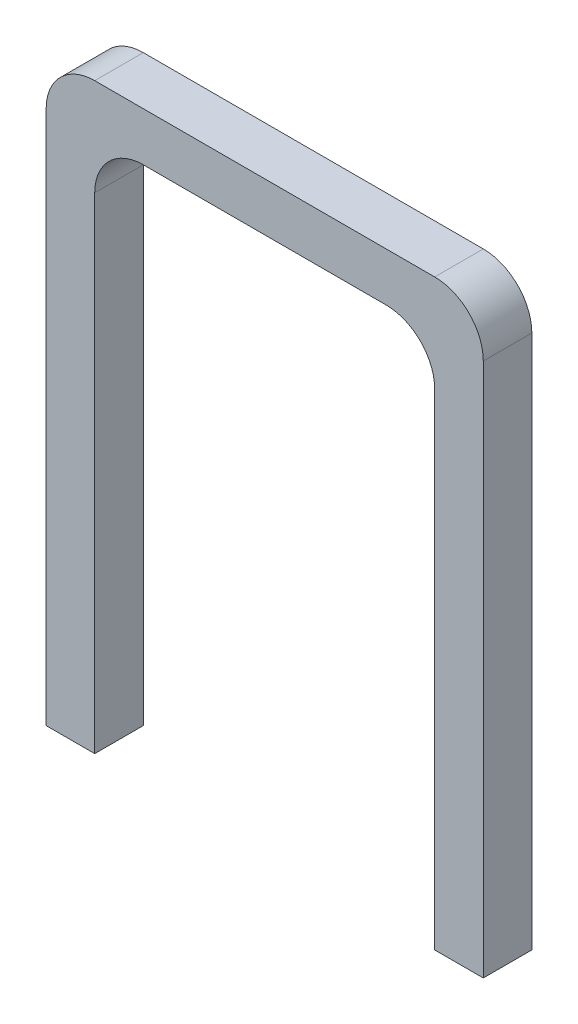
SolidWorks part; units mm, degrees
ref_plane "Front Plane" through (0, 0, 0) normal (0, 0, 1) x (1, 0, 0)
ref_plane "Top Plane" through (0, 0, 0) normal (0, 1, 0) x (1, 0, 0)
ref_plane "Right Plane" through (0, 0, 0) normal (1, 0, 0) x (0, 0, -1)
sketch "Sketch1" plane through (0, 0, 0) normal (0, 1, 0) x (1, 0, 0)
  line L1 (0, 0) -> (2, 0)
  line L2 (0, 0) -> (0, 2)
  line L3 (0, 2) -> (2, 2)
  line L4 (2, 0) -> (2, 2)
extrude "Boss-Extrude1" add sketch "Sketch1" along normal blind 24
sketch "Sketch2" plane through (2, 0, 0) normal (1, 0, 0) x (0, 0, -1)
  line L0 (2, 24) -> (2, 0) construction
  line L1 (0, 24) -> (2, 24)
  line L2 (0, 24) -> (0, 22)
  line L3 (0, 22) -> (2, 22)
  line L4 (2, 24) -> (2, 22)
  dimension "D1" = 2
extrude "Boss-Extrude2" add sketch "Sketch2" along normal blind 16
sketch "Sketch3" plane through (0, 22, 0) normal (0, -1, 0) x (-1, 0, 0)
  line L0 (-18, 2) -> (-2, 2) construction
  line L1 (-18, 0) -> (-16, 0)
  line L2 (-18, 0) -> (-18, 2)
  line L3 (-18, 2) -> (-16, 2)
  line L4 (-16, 0) -> (-16, 2)
extrude "Boss-Extrude3" add sketch "Sketch3" along normal blind 22
fillet "Fillet1" radius 2 2 edges at (16, 22, -1) (2, 22, -1)
fillet "Fillet2" radius 2 2 edges at (18, 24, -1) (0, 24, -1)
